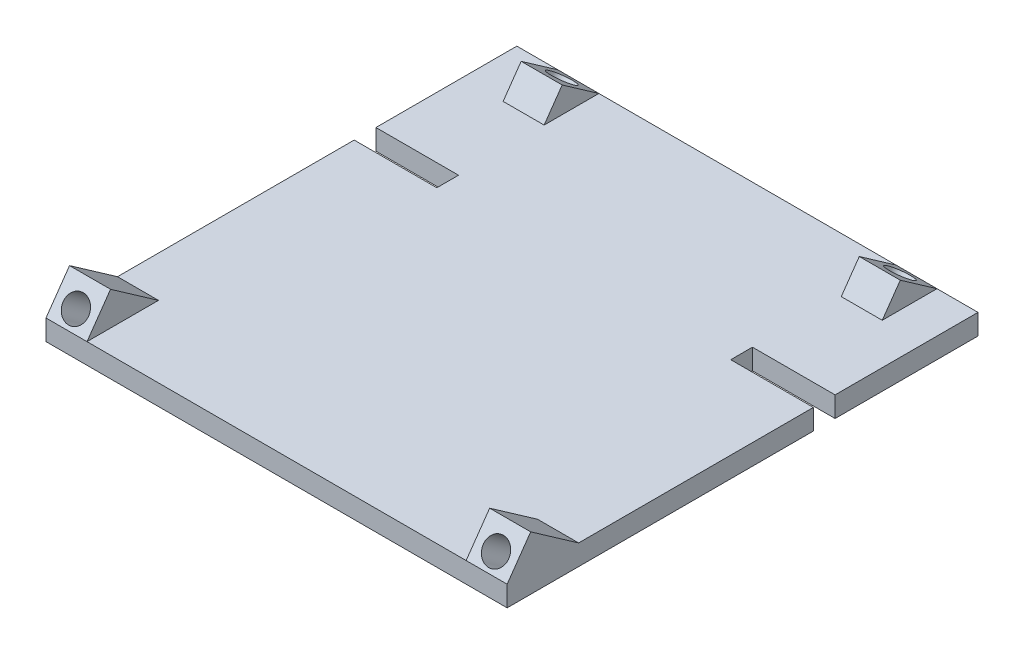
SolidWorks part; units mm, degrees
material "PET"
ref_plane "Front Plane" through (0, 0, 0) normal (0, 0, 1) x (1, 0, 0)
ref_plane "Top Plane" through (0, 0, 0) normal (0, 1, 0) x (1, 0, 0)
ref_plane "Right Plane" through (0, 0, 0) normal (1, 0, 0) x (0, 0, -1)
sketch "Sketch1" plane through (-32.812, 33.9517, -54.9073) normal (0, -1, 0) x (-1, 0, 0)
  line L1 (-55, 35) -> (57.4546, 35)
  line L2 (-55, 35) -> (-55, -85)
  line L3 (-55, -85) -> (57.4546, -85)
  line L4 (57.4546, 35) -> (57.4546, -85)
  line L19 (-34.85, -5.15) -> (-34.85, 0.15)
  line L20 (-34.85, 0.15) -> (-55.15, 0.15)
  line L21 (-55.15, 0.15) -> (-55.15, -5.15)
  line L22 (-55.15, -5.15) -> (-34.85, -5.15)
  line L31 (57.6046, -4.6732) -> (57.6046, 0.6268)
  line L32 (57.6046, 0.6268) -> (37.3046, 0.6268)
  line L33 (37.3046, 0.6268) -> (37.3046, -4.6732)
  line L34 (37.3046, -4.6732) -> (57.6046, -4.6732)
  dimension "D2" = 120
extrude "Boss-Extrude1" add sketch "Sketch1" along normal mid plane 5 contours L34 L33 L32 L4 L1 L2 L20 L19 L22 L3
sketch "Sketch2" plane through (-90.2666, 0, 0) normal (-1, 0, 0) x (0, 0, 1)
  line L0 (7.4822, 36.4517) -> (19.1809, 44.6433)
  line L2 (-50.2342, 36.4517) -> (30.0927, 36.4517) construction
  line L3 (19.1809, 44.6433) -> (24.9167, 36.4517)
  line L4 (19.833, 41.4375) -> (-62.0822, -15.9201) construction
  line L6 (23.2745, 36.5226) -> (19.833, 41.4375) construction
  line L7 (19.833, 41.4375) -> (-62.0822, -15.9201) construction
  line L8 (7.4822, 36.4517) -> (24.9167, 36.4517)
  dimension "D1" = 3
  dimension "D2" = 10
extrude "Boss-Extrude2" add sketch "Sketch2" against normal blind 10
sketch "Sketch3" plane through (0, 23.6993, 33.8461) normal (0, 0.5736, 0.8192) x (1, 0, 0)
  circle A2 centre (-85.2666, 19.5679) radius 3.1
  circle A3 centre (-85.2666, 19.5679) radius 3.1
  dimension "D1" = 0
extrude "Cut-Extrude1" cut sketch "Sketch3" against normal through all
ref_plane "Plane1" through (-70.2666, 0, 0) normal (1, 0, 0) x (0, 0, -1)
sketch "Sketch4" plane through (-70.2666, 0, 0) normal (1, 0, 0) x (0, 0, -1)
  line L0 (76.5597, 36.4517) -> (80.9509, 42.7231)
  line L1 (89.9073, 36.4517) -> (55.0573, 36.4517) construction
  line L2 (80.9509, 42.7231) -> (89.9073, 36.4517)
  line L3 (157.7666, 147.1969) -> (43.0513, -16.6335) construction
  line L4 (157.7666, 147.1969) -> (43.0513, -16.6335) construction
  line L5 (76.5597, 36.4517) -> (89.9073, 36.4517)
  dimension "D1" = 3
extrude "Boss-Extrude3" add sketch "Sketch4" against normal blind 10
sketch "Sketch5" plane through (0, 66.7021, -46.7053) normal (0, 0.8192, -0.5736) x (1, 0, 0)
  circle A0 centre (-75.2666, 47.8062) radius 3.1
  dimension "D1" = 6.2
extrude "Cut-Extrude2" cut sketch "Sketch5" against normal through all
ref_plane "Plane2" through (-34.0393, 0, 0) normal (-1, 0, 0) x (0, 0, 1)
mirror "Mirror1" about plane through (-34.0393, 0, 0) normal (-1, 0, 0) of "Cut-Extrude2", "Boss-Extrude3", "Cut-Extrude1", "Boss-Extrude2"
sketch "Sketch6" plane through (-90.2666, 0, 0) normal (-1, 0, 0) x (0, 0, 1)
  line L7 (24.9167, 36.4517) -> (24.9167, 31.4517)
  line L8 (24.9167, 31.4517) -> (-55.3238, 31.4517)
  line L14 (7.4822, 36.4517) -> (-50.2342, 36.4517)
  line L15 (-50.2342, 36.4517) -> (-50.2342, 31.4517)
  line L17 (-50.2342, 36.4517) -> (-50.2342, 31.4517)
  line L19 (24.9167, 36.4517) -> (19.1809, 44.6433)
  line L20 (19.1809, 44.6433) -> (7.4822, 36.4517)
  line L21 (7.4822, 36.4517) -> (-50.2342, 36.4517)
  line L26 (24.9167, 36.4517) -> (19.1809, 44.6433)
  line L27 (19.1809, 44.6433) -> (7.4822, 36.4517)
  line L30 (-50.2342, 31.4517) -> (30.0927, 31.4517)
  line L32 (-50.2342, 31.4517) -> (30.0927, 31.4517)
  line L34 (30.0927, 31.4517) -> (30.0927, 36.4517)
  line L35 (30.0927, 31.4517) -> (30.0927, 36.4517)
  line L36 (30.0927, 36.4517) -> (24.9167, 36.4517)
  line L37 (30.0927, 36.4517) -> (24.9167, 36.4517)
  line M10 (-50.2342, 31.4517) -> (30.0927, 31.4517)
  line M11 (30.0927, 31.4517) -> (30.0927, 36.4517)
  line M12 (30.0927, 36.4517) -> (24.9167, 36.4517)
  dimension "D1" = 0
extrude "Cut-Extrude3" cut sketch "Sketch6" against normal through all contours L7 M12 M10 M11
